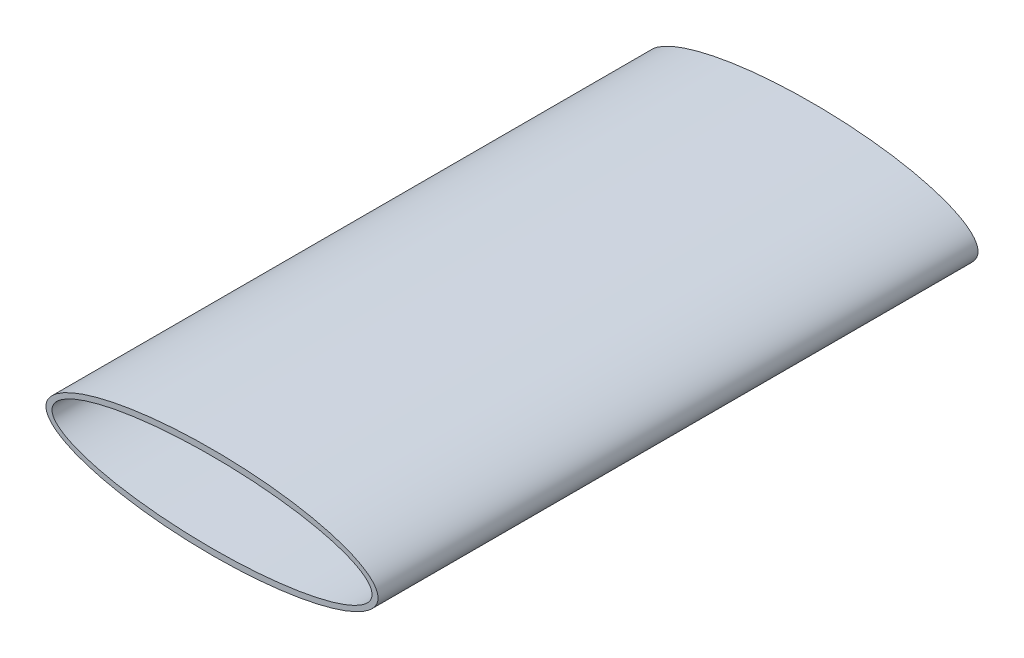
SolidWorks part; units mm, degrees
ref_plane "Plane1" through (0, 0, 0) normal (0, 0, 1) x (1, 0, 0)
ref_plane "Plane2" through (0, 0, 0) normal (0, 1, 0) x (1, 0, 0)
ref_plane "Plane3" through (0, 0, 0) normal (1, 0, 0) x (0, 0, -1)
sketch "Эскиз1" plane through (0, 0, 0) normal (0, 0, 1) x (1, 0, 0)
  ellipse E0 centre (1000, 400) end of major axis (170, 400) minor radius 230
  ellipse E1 centre (1000, 400) end of major axis (200, 400) minor radius 200
extrude "Вытянуть1" add sketch "Эскиз1" against normal blind 3000
